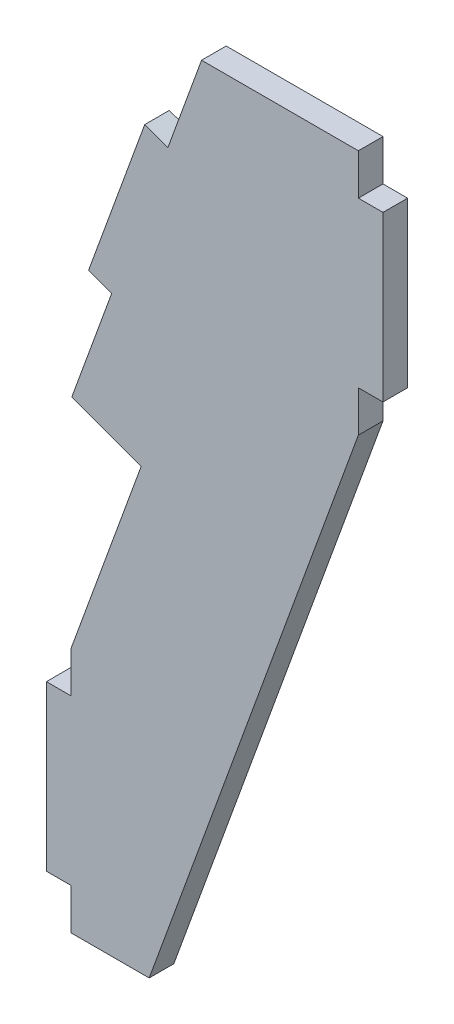
SolidWorks part; units mm, degrees
ref_plane "Front Plane" through (0, 0, 0) normal (0, 0, 1) x (1, 0, 0)
ref_plane "Top Plane" through (0, 0, 0) normal (0, 1, 0) x (1, 0, 0)
ref_plane "Right Plane" through (0, 0, 0) normal (1, 0, 0) x (0, 0, -1)
sketch "Sketch1" plane through (0, 0, 0) normal (0, 0, 1) x (1, 0, 0)
  line L0 (3, -5) -> (12.5221, -5)
  line L1 (38, 95) -> (28.4779, 95)
  line L32 (3, 20) -> (0, 20)
  line L33 (0, 20) -> (0, 0)
  line L34 (0, 0) -> (3, 0)
  line L35 (3, 0) -> (3, -5)
  line L36 (12.5221, -5) -> (38, 65)
  line L37 (38, 65) -> (38, 70)
  line L38 (38, 70) -> (41, 70)
  line L39 (41, 70) -> (41, 90)
  line L40 (41, 90) -> (38, 90)
  line L41 (38, 90) -> (38, 95)
  line L42 (28.4779, 95) -> (18.3909, 67.2862)
  line L43 (18.3909, 67.2862) -> (15.5718, 68.3122)
  line L44 (15.5718, 68.3122) -> (8.7314, 49.5184)
  line L45 (8.7314, 49.5184) -> (11.5505, 48.4923)
  line L46 (11.5505, 48.4923) -> (3, 25)
  line L47 (3, 25) -> (3, 20)
  dimension "D1" = 20
  dimension "D2" = 3
  dimension "D3" = 90
  dimension "D4" = 20
  dimension "D5" = 3
  dimension "D6" = 38
  dimension "D7" = 20
  dimension "D8" = 5
  dimension "D9" = 5
  dimension "D10" = 5
  dimension "D11" = 20
  dimension "D12" = 3
  dimension "D13" = 5
  dimension "D14" = 25
extrude "Boss-Extrude1" add sketch "Sketch1" along normal blind 3
sketch "Sketch2" plane through (0, 0, 0) normal (0, 0, -1) x (-1, 0, 0)
  line L1 (-7.9557, 64.9298) -> (-3.0933, 51.5705)
  line L3 (-7.9557, 64.9298) -> (-5.1366, 65.9559)
  line L5 (-5.1366, 65.9559) -> (-11.977, 84.7497)
  line L7 (-11.977, 84.7497) -> (-14.7961, 83.7237)
  line L8 (-14.7961, 83.7237) -> (-18.9003, 95)
  line L9 (-18.9003, 95) -> (-28.4779, 95)
  line L10 (-28.4779, 95) -> (-18.3909, 67.2862)
  line L11 (-18.3909, 67.2862) -> (-15.5718, 68.3122)
  line L12 (-15.5718, 68.3122) -> (-8.7314, 49.5184)
  line L13 (-3.0933, 51.5705) -> (-8.7314, 49.5184)
  dimension "D1" = 12
  dimension "D2" = 3
  dimension "D3" = 3
  dimension "D4" = 20
  dimension "D5" = 12
extrude "Boss-Extrude2" add sketch "Sketch2" against normal up to vertex (3 mm away)
